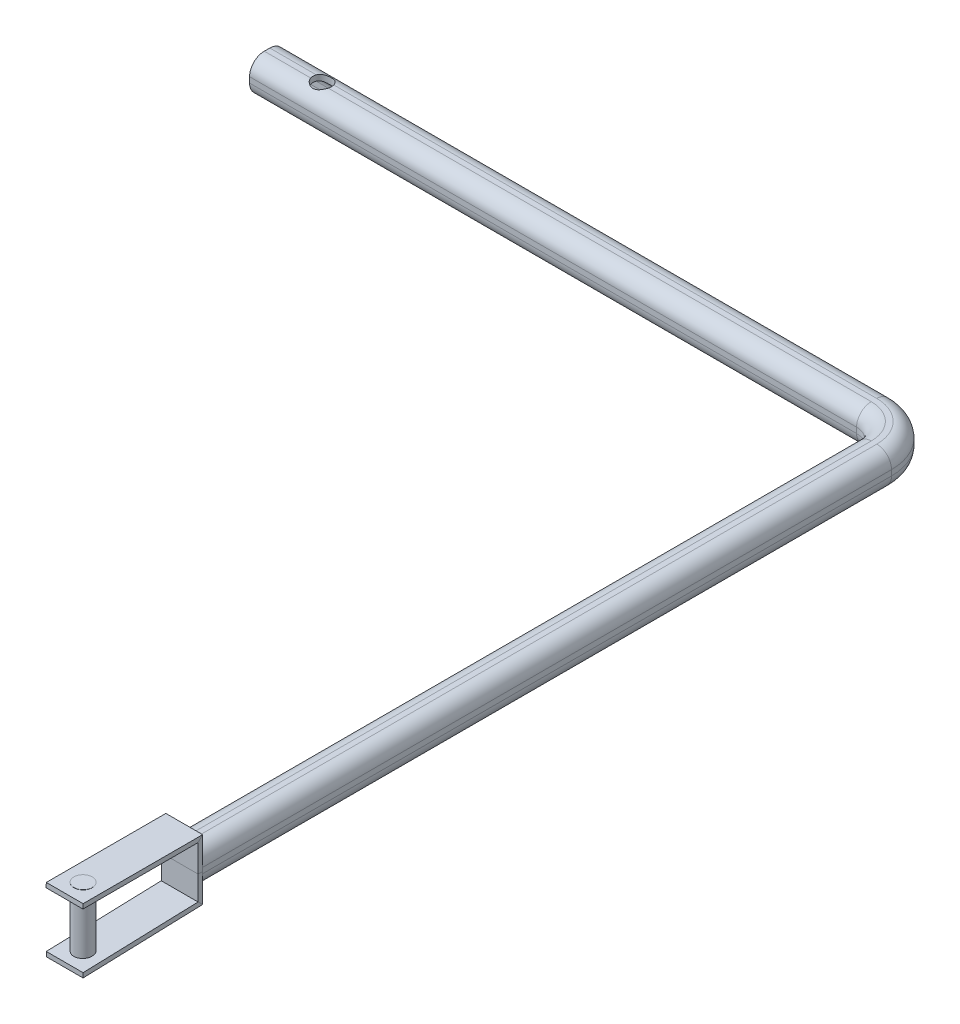
SolidWorks part; units mm, degrees
ref_plane "Front Plane" through (0, 0, 0) normal (0, 0, 1) x (1, 0, 0)
ref_plane "Top Plane" through (0, 0, 0) normal (0, 1, 0) x (1, 0, 0)
ref_plane "Right Plane" through (0, 0, 0) normal (1, 0, 0) x (0, 0, -1)
sketch "Sketch1" plane through (0, 0, 0) normal (0, 1, 0) x (1, 0, 0)
  line L0 (0, 0) -> (330, 0)
  line L1 (350, -20) -> (350, -395)
  arc A0 (350, -20) -> (330, 0) centre (330, -20) ccw
  point P6 (350, 0)
  dimension "D3" = 20
  dimension "D1" = 350
  dimension "D2" = 395
sketch "Sketch2" plane through (0, 0, 0) normal (1, 0, 0) x (0, 0, -1)
  line L1 (-1.5, -6.5) -> (1.5, -6.5)
  line L2 (-6.5, -1.5) -> (-6.5, 1.5)
  line L3 (-1.5, 6.5) -> (1.5, 6.5)
  line L4 (6.5, -1.5) -> (6.5, 1.5)
  line L5 (-6.5, -6.5) -> (6.5, 6.5) construction
  line L6 (-6.5, 6.5) -> (6.5, -6.5) construction
  arc A0 (6.5, -1.5) -> (1.5, -6.5) centre (1.5, -1.5) cw
  arc A1 (-1.5, -6.5) -> (-6.5, -1.5) centre (-1.5, -1.5) cw
  arc A2 (-6.5, 1.5) -> (-1.5, 6.5) centre (-1.5, 1.5) cw
  arc A3 (1.5, 6.5) -> (6.5, 1.5) centre (1.5, 1.5) cw
  point P0 (0, 0)
  dimension "D3" = 5
  dimension "D1" = 13
  dimension "D2" = 13
sketch "Sketch3" plane through (0, 0, 0) normal (0, 1, 0) x (1, 0, 0)
  line L0 (350, -413.3468) -> (350, -478.5519) construction
  line L1 (350, -20) -> (350, -395) construction
  circle A0 centre (350, -450) radius 50
  dimension "D1" = 100
  dimension "D2" = 55
sweep "Sweep-Thin1" add profiles "Sketch2" path "Sketch1" parameters "D1"=3
sketch "Sketch4" plane through (0, 0, 0) normal (0, 1, 0) x (1, 0, 0)
  circle A0 centre (350, -450) radius 5
extrude "Boss-Extrude2" add sketch "Sketch4" along normal blind 17.5 and the other way blind 17.5
ref_plane "Plane1" through (350, 0, 0) normal (1, 0, 0) x (0, 0, -1)
sketch "Sketch6" plane through (350, 0, 0) normal (1, 0, 0) x (0, 0, -1)
  line L0 (-395, 17.4) -> (-460, 17.4)
  line L1 (-395, 0) -> (-395, 17.4)
  line L2 (-20, 0) -> (-395, 0) construction
  line L3 (-395, 0) -> (-395, -15.4852)
  line L4 (-395, -15.4852) -> (-460, -17.6)
  dimension "D1" = 65
  dimension "D2" = 15.4852
  dimension "D3" = 17.4
ref_plane "Plane2" through (0, 0, 460) normal (0, 0, 1) x (1, 0, 0)
sketch "Sketch7" plane through (0, 0, 460) normal (0, 0, 1) x (1, 0, 0)
  line L0 (350, -17.6) -> (350, 17.4) construction
  line L2 (360, -15.1) -> (340, -15.1)
  line L3 (360, -15.1) -> (360, -17.6)
  line L4 (360, -17.6) -> (340, -17.6)
  line L5 (340, -15.1) -> (340, -17.6)
  line L6 (360, -15.1) -> (340, -17.6) construction
  line L7 (360, -17.6) -> (340, -15.1) construction
  point P2 (350, -16.35)
  dimension "D1" = 20
  dimension "D2" = 2.5
sweep "Sweep1" add profiles "Sketch7" path "Sketch6"
sketch "Sketch8" plane through (0, 0, 0) normal (0, 1, 0) x (1, 0, 0)
  line L0 (330, 0) -> (30, 0) construction
  line L1 (0, 0) -> (330, 0) construction
  circle A0 centre (30, 0) radius 5
  dimension "D4" = 10
  dimension "D1" = 300
extrude "Cut-Extrude1" cut sketch "Sketch8" against normal through all both and the other way through all
ref_plane "Plane3" through (0, 0, 0) normal (0, 1, 0) x (1, 0, 0)
sketch "Sketch9" plane through (0, 0, 0) normal (0, 1, 0) x (1, 0, 0)
  line L0 (350, -450) -> (-350, -450) construction
  line L1 (-350, -450) -> (-350, -239.3388) construction
  dimension "D1" = 700
